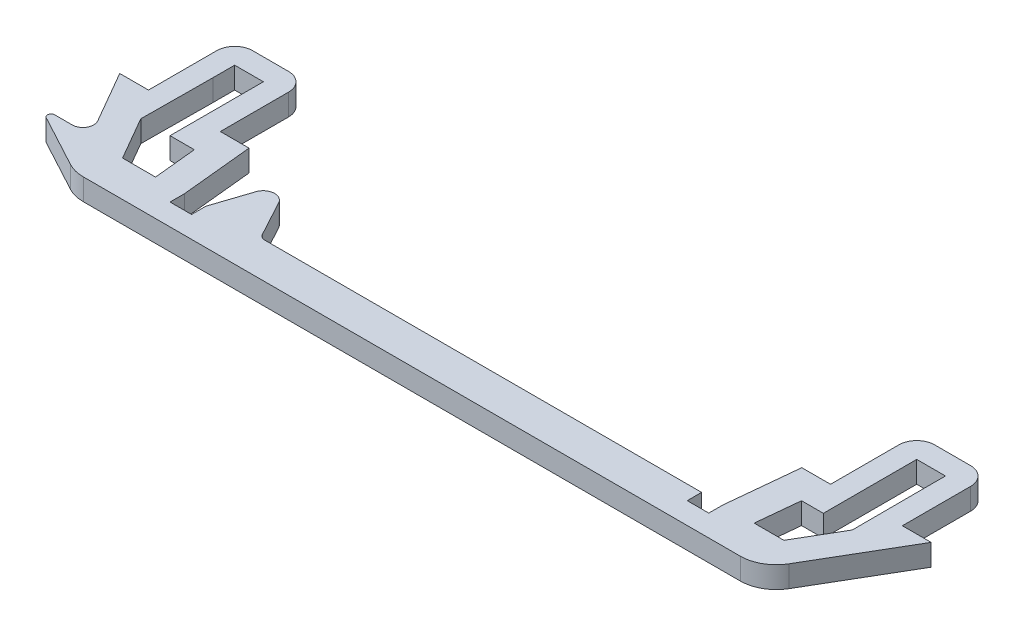
SolidWorks part; units mm, degrees
material "Custom Plastic"
ref_plane "Front Plane" through (0, 0, 0) normal (0, 0, 1) x (1, 0, 0)
ref_plane "Top Plane" through (0, 0, 0) normal (0, 1, 0) x (1, 0, 0)
ref_plane "Right Plane" through (0, 0, 0) normal (1, 0, 0) x (0, 0, -1)
sketch "Sketch1" plane through (0, 0, 0) normal (0, 1, 0) x (1, 0, 0)
  line L0 (-62.4186, -50.1587) -> (-58.4186, -50.1587)
  line L1 (-58.4186, -50.1587) -> (-58.4186, -38.1587)
  line L2 (-58.4186, -38.1587) -> (-48.4186, -38.1587)
  line L3 (-48.4186, -38.1587) -> (-48.4186, -50.1587)
  line L4 (-48.4186, -50.1587) -> (-44.4186, -50.1587)
  line L5 (-44.4186, -50.1587) -> (-43.4188, -60.1562)
  line L7 (31.5814, -60.2088) -> (32.5814, -50.2113)
  line L8 (32.5814, -50.2113) -> (36.5814, -50.2113)
  line L9 (36.5814, -50.2113) -> (36.5814, -38.2113)
  line L10 (36.5814, -38.2113) -> (46.5814, -38.2113)
  line L11 (46.5814, -38.2113) -> (46.5814, -50.2113)
  line L12 (46.5814, -50.2113) -> (50.5814, -50.2113)
  line L13 (50.5814, -50.2113) -> (41.8306, -65.1587)
  line L14 (41.8306, -65.1587) -> (-53.7583, -65.1587)
  line L15 (-58.2259, -57.4205) -> (-62.4186, -50.1587)
  line L16 (36.5478, -54.2113) -> (39.5814, -54.2113)
  line L17 (-55.4186, -41.1587) -> (-51.4186, -41.1587)
  line L18 (-55.4186, -41.1587) -> (-55.4186, -44.1587)
  line L20 (-51.4186, -41.1587) -> (-51.4186, -44.1587)
  line L21 (39.5814, -41.2113) -> (43.5814, -41.2113)
  line L22 (39.5814, -41.2113) -> (39.5814, -44.2113)
  line L24 (43.5814, -41.2113) -> (43.5814, -44.2113)
  line L25 (43.6046, -54.2113) -> (40.0934, -60.2088)
  line L26 (40.0934, -60.2088) -> (35.9479, -60.2088)
  line L27 (35.9479, -60.2088) -> (36.5478, -54.2113)
  line L28 (-51.4186, -54.1587) -> (-48.0385, -54.1587)
  line L29 (-48.0385, -54.1587) -> (-47.4385, -60.1587)
  line L30 (-47.4385, -60.1587) -> (-52.0263, -60.1587)
  line L31 (-52.0263, -60.1587) -> (-55.4904, -54.1587)
  line L32 (28.5814, -60.1587) -> (28.5814, -62.1587)
  line L33 (28.5814, -47.1587) -> (28.5814, -62.1587) construction
  line L34 (28.5814, -62.1587) -> (31.5814, -62.1587)
  line L35 (31.5814, -62.1587) -> (31.5814, -60.2088)
  line L36 (31.5814, -62.1587) -> (31.5814, -47.1587) construction
  line L38 (-43.4188, -60.1562) -> (-43.4188, -62.1587)
  line L39 (-43.4188, -62.1587) -> (-40.4188, -62.1587)
  line L40 (-40.4188, -62.1587) -> (-40.4188, -60.1587)
  line L41 (-32.8035, -60.1587) -> (28.5814, -60.1587)
  line L42 (-32.8035, -60.1587) -> (-35.7725, -54.6685)
  line L43 (43.5814, -44.2113) -> (43.6046, -54.2113)
  line L44 (-38.6829, -54.9246) -> (-40.4188, -60.1587)
  line L45 (39.5814, -44.2113) -> (39.5814, -54.2113)
  line L46 (-55.4186, -44.1587) -> (-55.4904, -54.1587)
  line L47 (-51.4186, -44.1587) -> (-51.4186, -54.1587)
  line L48 (-53.7583, -65.1587) -> (-62.2024, -60.6107)
  line L49 (-61.9653, -59.6705) -> (-59.525, -59.6705)
  arc A0 (-38.6829, -54.9246) -> (-35.7725, -54.6685) centre (-37.1723, -55.4255) cw
  arc A1 (-59.525, -59.6705) -> (-58.2259, -57.4205) centre (-59.525, -58.1705) ccw
  arc A2 (-62.2024, -60.6107) -> (-61.9653, -59.6705) centre (-61.9653, -60.1705) cw
  dimension "D6" = 0.5
  dimension "D5" = 1.5
  dimension "D1" = 15
  dimension "D2" = 4
  dimension "D3" = 12
  dimension "D4" = 3
  dimension "D7" = 120
  dimension "D8" = 10
  dimension "D9" = 85
  dimension "D10" = 3
  dimension "D11" = 95.5889
  dimension "D12" = 3
  dimension "D13" = 3
  dimension "D14" = 3
  dimension "D15" = 3
  dimension "D17" = 4
  dimension "D18" = 4
  dimension "D19" = 4
  dimension "D20" = 4
  dimension "D21" = 4
  dimension "D23" = 2
  dimension "D24" = 3
extrude "Boss-Extrude1" add sketch "Sketch1" along normal blind 3
fillet "Fillet1" radius 5 2 edges at (41.8306, 1.5, 65.1587) (-53.7583, 1.5, 65.1587)
fillet "Fillet2" radius 2.5 4 edges at (46.5814, 1.5, 38.2113) (36.5814, 1.5, 38.2113) (-58.4186, 1.5, 38.1587) (-48.4186, 1.5, 38.1587)
fillet "Fillet3" radius 1 1 edges at (-32.8035, 1.5, 60.1587)
